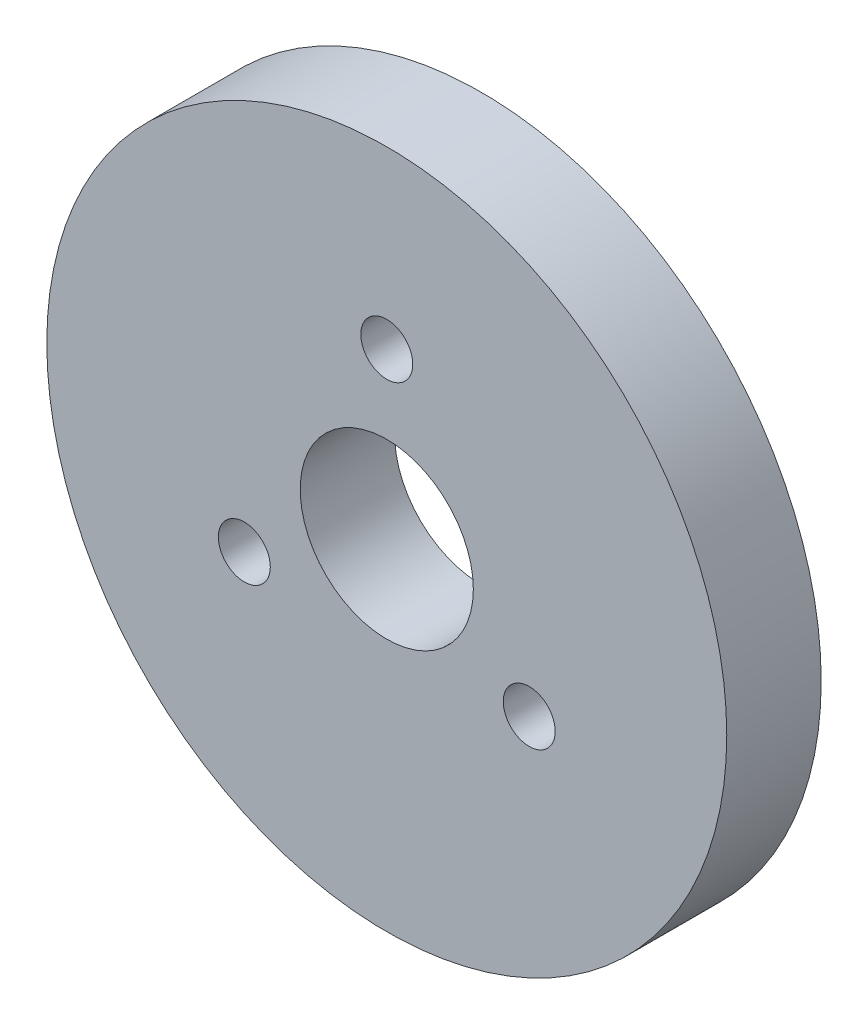
SolidWorks part; units mm, degrees
ref_plane "Front Plane" through (0, 0, 0) normal (0, 0, 1) x (1, 0, 0)
ref_plane "Top Plane" through (0, 0, 0) normal (0, 1, 0) x (1, 0, 0)
ref_plane "Right Plane" through (0, 0, 0) normal (1, 0, 0) x (0, 0, -1)
sketch "Sketch1" plane through (0, 0, 0) normal (0, 0, 1) x (1, 0, 0)
  circle A0 centre (0, 0) radius 21.6
  circle A1 centre (0, 0) radius 5.5
  dimension "D1" = 43.2
  dimension "D2" = 11
extrude "Boss-Extrude1" add sketch "Sketch1" along normal blind 6
sketch "Sketch2" plane through (0, 0, 6) normal (0, 0, 1) x (1, 0, 0)
  line L0 (0, 0) -> (0, 50000) construction
  line L1 (0, 0) -> (50000, 0) construction
  circle A0 centre (0, 10.45) radius 1.65
  circle A1 centre (0, 0) radius 5.5 construction
  circle A2 centre (9.05, -5.225) radius 1.65
  circle A3 centre (-9.05, -5.225) radius 1.65
  point P16 (0, 0)
  dimension "D1" = 3.3
  dimension "D2" = 10.45
  dimension "D3" = 3
extrude "Cut-Extrude1" cut sketch "Sketch2" against normal through all
